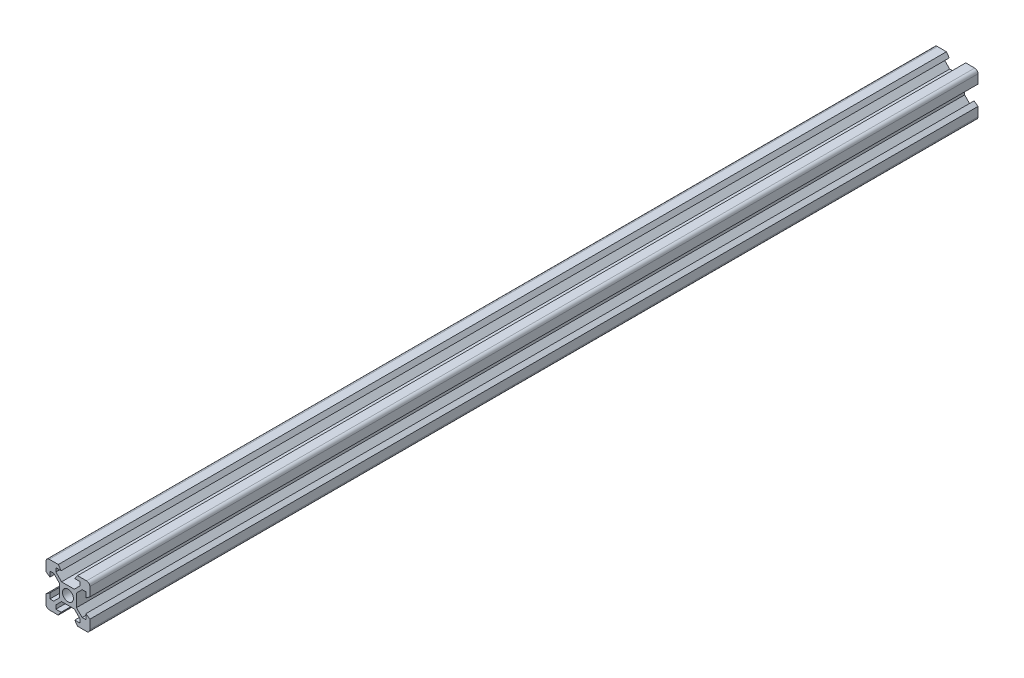
SolidWorks part; units mm, degrees
ref_plane "前视基准面" through (0, 0, 0) normal (0, 0, 1) x (1, 0, 0)
ref_plane "上视基准面" through (0, 0, 0) normal (0, 1, 0) x (1, 0, 0)
ref_plane "右视基准面" through (0, 0, 0) normal (1, 0, 0) x (0, 0, -1)
sketch "草图1" plane through (0, 0, 0) normal (0, 0, 1) x (1, 0, 0)
  line L0 (16.8101, 19.3214) -> (19.4, 21.9114) construction
  line L1 (14.8, 34.8214) -> (18.9, 34.8214)
  line L2 (13.3, 33.3214) -> (13.3, 29.2214)
  line L3 (14.8, 14.8214) -> (18.9, 14.8214)
  line L4 (33.3, 33.3214) -> (33.3, 29.2214)
  line L7 (27.2, 27.7315) -> (29.7899, 30.3214) construction
  line L8 (33.3, 29.2214) -> (31.5, 27.9214)
  line L9 (28.8, 31.3114) -> (26.2101, 28.7214)
  line L10 (31.5, 30.3214) -> (31.5, 27.9214)
  line L11 (29.7899, 30.3214) -> (31.5, 30.3214)
  line L12 (26.2101, 28.7214) -> (28.8, 31.3114) construction
  line L13 (27.2, 27.7315) -> (29.7899, 30.3214)
  line L15 (20.3899, 28.7214) -> (26.2101, 28.7214) construction
  line L18 (18.9, 34.8214) -> (20.2, 33.0214)
  line L19 (27.7, 34.8214) -> (26.4, 33.0214)
  line L20 (26.4, 33.0214) -> (28.8, 33.0214)
  line L21 (28.8, 33.0214) -> (28.8, 31.3114)
  line L22 (26.2101, 28.7214) -> (20.3899, 28.7214)
  line L25 (20.3899, 28.7214) -> (17.8, 31.3114)
  line L26 (17.8, 31.3114) -> (17.8, 33.0214)
  line L27 (17.8, 33.0214) -> (20.2, 33.0214)
  line L28 (27.2, 21.9114) -> (27.2, 27.7315)
  line L29 (29.7899, 19.3214) -> (27.2, 21.9114)
  line L30 (31.5, 19.3214) -> (29.7899, 19.3214)
  line L31 (31.5, 21.7214) -> (31.5, 19.3214)
  line L32 (33.3, 20.4214) -> (31.5, 21.7214)
  line L33 (27.7, 14.8214) -> (26.4, 16.6214)
  line L34 (28.8, 16.6214) -> (26.4, 16.6214)
  line L35 (28.8, 18.3315) -> (28.8, 16.6214)
  line L36 (26.2101, 20.9214) -> (28.8, 18.3315)
  line L37 (20.3899, 20.9214) -> (26.2101, 20.9214)
  line L38 (17.8, 18.3315) -> (20.3899, 20.9214)
  line L39 (17.8, 16.6214) -> (17.8, 18.3315)
  line L40 (20.2, 16.6214) -> (17.8, 16.6214)
  line L41 (18.9, 14.8214) -> (20.2, 16.6214)
  line L42 (13.3, 20.4214) -> (15.1, 21.7214)
  line L43 (15.1, 19.3214) -> (15.1, 21.7214)
  line L44 (16.8101, 19.3214) -> (15.1, 19.3214)
  line L45 (19.4, 21.9114) -> (16.8101, 19.3214)
  line L46 (19.4, 27.7315) -> (19.4, 21.9114)
  line L47 (16.8101, 30.3214) -> (19.4, 27.7315)
  line L48 (15.1, 30.3214) -> (16.8101, 30.3214)
  line L49 (15.1, 27.9214) -> (15.1, 30.3214)
  line L50 (13.3, 29.2214) -> (15.1, 27.9214)
  line L51 (27.7, 34.8214) -> (31.8, 34.8214)
  line L52 (33.3, 20.4214) -> (33.3, 16.3214)
  line L53 (13.3, 20.4214) -> (13.3, 16.3214)
  line L54 (27.7, 14.8214) -> (31.8, 14.8214)
  circle A0 centre (23.3, 24.8214) radius 2.5
  arc A1 (14.8, 34.8214) -> (13.3, 33.3214) centre (14.8, 33.3214) ccw
  arc A2 (33.3, 33.3214) -> (31.8, 34.8214) centre (31.8, 33.3214) ccw
  arc A3 (31.8, 14.8214) -> (33.3, 16.3214) centre (31.8, 16.3214) ccw
  arc A4 (14.8, 14.8214) -> (13.3, 16.3214) centre (14.8, 16.3214) cw
  point P11 (33.3, 34.8214)
  point P18 (33.3, 14.8214)
  dimension "D3" = 5
  dimension "D1" = 1.5
  dimension "D4" = 1.5
  dimension "D5" = 1.5
  dimension "D7" = 1.5
  dimension "D2" = 20
  dimension "D6" = 4
extrude "凸台-拉伸1" add sketch "草图1" along normal blind 405
